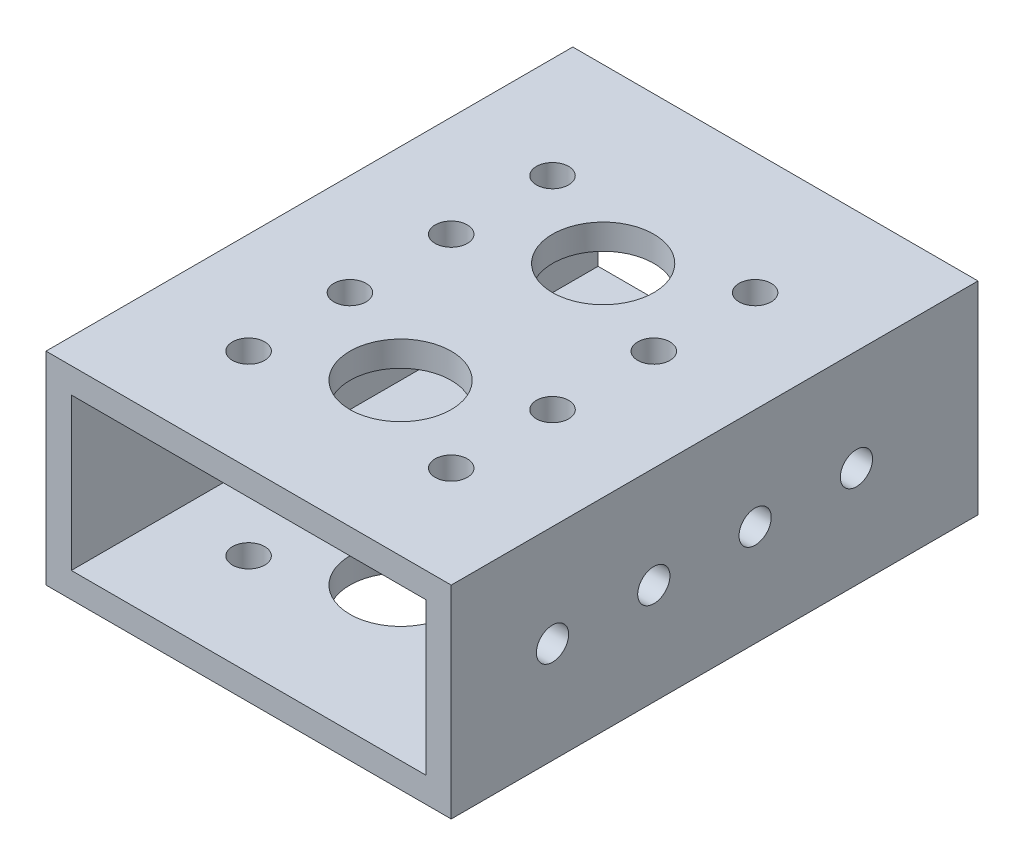
SolidWorks part; units mm, degrees
material "6061 Alloy"
ref_plane "Front Plane" through (0, 0, 0) normal (0, 0, 1) x (1, 0, 0)
ref_plane "Top Plane" through (0, 0, 0) normal (0, 1, 0) x (1, 0, 0)
ref_plane "Right Plane" through (0, 0, 0) normal (1, 0, 0) x (0, 0, -1)
sketch "Sketch1" plane through (0, 0, 0) normal (0, 0, 1) x (1, 0, 0)
  line L0 (3.175, 22.225) -> (47.625, 22.225)
  line L1 (0, 0) -> (50.8, 0)
  line L2 (0, 0) -> (0, 25.4)
  line L3 (0, 25.4) -> (50.8, 25.4)
  line L4 (50.8, 0) -> (50.8, 25.4)
  line L5 (47.625, 3.175) -> (47.625, 22.225)
  line L6 (3.175, 3.175) -> (47.625, 3.175)
  line L7 (3.175, 3.175) -> (3.175, 22.225)
  dimension "D1" = 50.8
  dimension "D2" = 25.4
  dimension "D3" = 3.175
extrude "Boss-Extrude1" add sketch "Sketch1" along normal blind 66.04
sketch "Sketch2" plane through (0, 25.4, 0) normal (0, 1, 0) x (1, 0, 0)
  line L0 (25.4, -66.04) -> (25.4, -15.24) construction
  line L1 (50.8, -66.04) -> (0, -66.04) construction
  line L3 (12.7, -53.34) -> (12.7, -40.64) construction
  line L4 (0, -66.04) -> (12.7, -66.04) construction
  line L5 (0, -66.04) -> (0, -53.34) construction
  line L6 (0, -53.34) -> (12.7, -53.34) construction
  line L7 (12.7, -66.04) -> (12.7, -53.34) construction
  line L8 (25.4, -46.99) -> (25.4, -21.59) construction
  circle A0 centre (12.7, -53.34) radius 2.0193
  circle A1 centre (25.4, -46.99) radius 6.35
  circle A2 centre (38.1, -53.34) radius 2.0193
  circle A3 centre (12.7, -40.64) radius 2.0193
  circle A4 centre (38.1, -40.64) radius 2.0193
  circle A5 centre (12.7, -27.94) radius 2.0193
  circle A6 centre (38.1, -27.94) radius 2.0193
  circle A7 centre (12.7, -15.24) radius 2.0193
  circle A8 centre (38.1, -15.24) radius 2.0193
  circle A11 centre (25.4, -21.59) radius 6.35
  circle A12 centre (12.7, -2.54) radius 2.0193 [skipped]
  circle A13 centre (38.1, -2.54) radius 2.0193 [skipped]
  dimension "D3" = 4.0386
  dimension "D4" = 12.7
  dimension "D1" = 12.7
  dimension "D2" = 12.7
  dimension "D5" = 19.05
  dimension "D7" = 12.7
  dimension "D9" = 25.4
  dimension "D6" = 5
  dimension "D8" = 2
extrude "Cut-Extrude1" cut sketch "Sketch2" against normal blind 63.5
sketch "Sketch3" plane through (50.8, 0, 0) normal (1, 0, 0) x (0, 0, -1)
  line L0 (-66.04, 12.7) -> (-14.7193, 12.7) construction
  line L1 (-66.04, 0) -> (-66.04, 25.4) construction
  line L2 (0, 0) -> (0, 25.4) construction
  line L3 (-53.34, 12.7) -> (-40.64, 12.7) construction
  line L4 (-10.6807, 12.7) -> (0, 12.7) construction
  circle A0 centre (-53.34, 12.7) radius 2.0193
  circle A1 centre (-40.64, 12.7) radius 2.0193
  circle A2 centre (-27.94, 12.7) radius 2.0193
  circle A3 centre (-15.24, 12.7) radius 2.0193
  arc A5 (-0.5207, 12.7) -> (-4.5593, 12.7) centre (-2.54, 12.7) ccw [skipped]
  dimension "D1" = 4.0386
  dimension "D2" = 12.7
  dimension "D4" = 12.7
  dimension "D3" = 5
extrude "Cut-Extrude2" cut sketch "Sketch3" against normal blind 63.5
